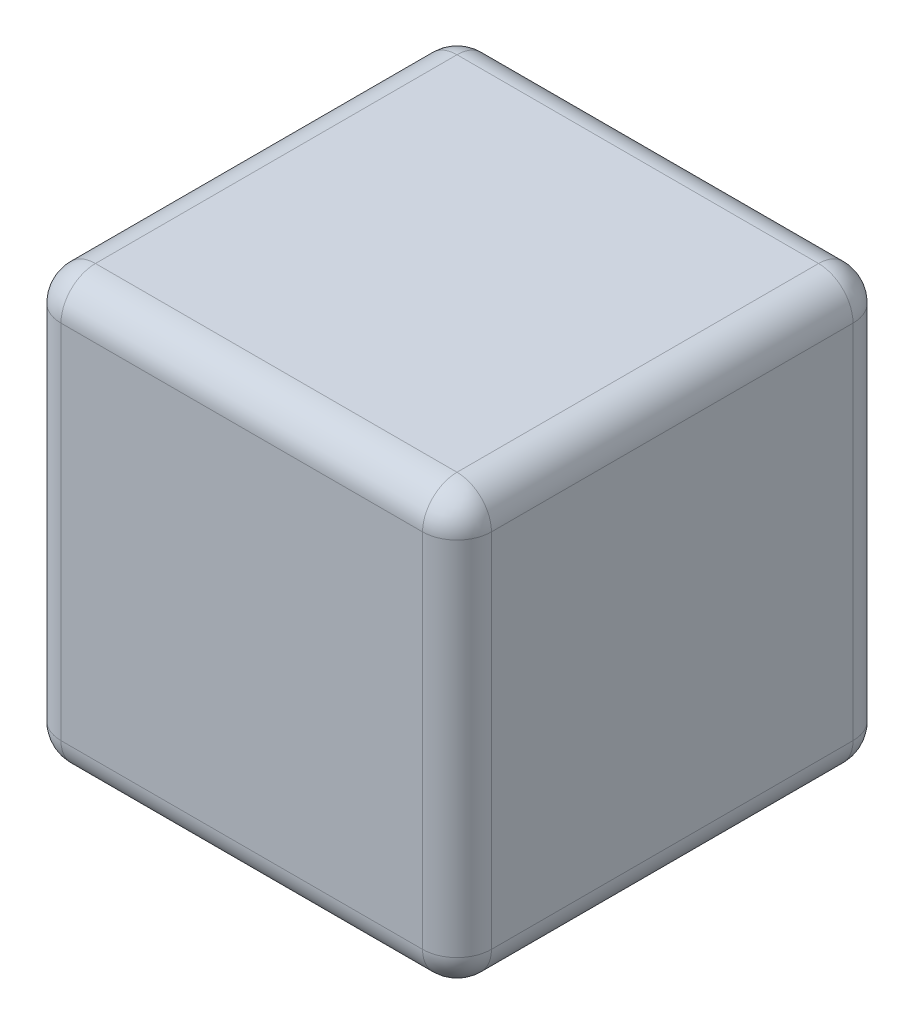
SolidWorks part; units mm, degrees
ref_plane "Front Plane" through (0, 0, 0) normal (0, 0, 1) x (1, 0, 0)
ref_plane "Top Plane" through (0, 0, 0) normal (0, 1, 0) x (1, 0, 0)
ref_plane "Right Plane" through (0, 0, 0) normal (1, 0, 0) x (0, 0, -1)
sketch "Sketch1" plane through (0, 0, 0) normal (0, 1, 0) x (1, 0, 0)
  line L0 (0, 0) -> (0, 31.75)
  line L1 (0, 31.75) -> (31.75, 31.75)
  line L2 (31.75, 31.75) -> (31.75, 0)
  line L3 (31.75, 0) -> (0, 0)
  dimension "D1" = 31.75
extrude "Boss-Extrude1" add sketch "Sketch1" along normal blind 31.75
fillet "Fillet2" radius 2.54 12 edges at (15.875, 0, 0) (0, 15.875, 0) (0, 0, -15.875) (0, 15.875, -31.75) (15.875, 0, -31.75) (0, 31.75, -15.875) (15.875, 31.75, -31.75) (15.875, 31.75, 0) (31.75, 15.875, 0) (31.75, 31.75, -15.875) (31.75, 15.875, -31.75) (31.75, 0, -15.875)
